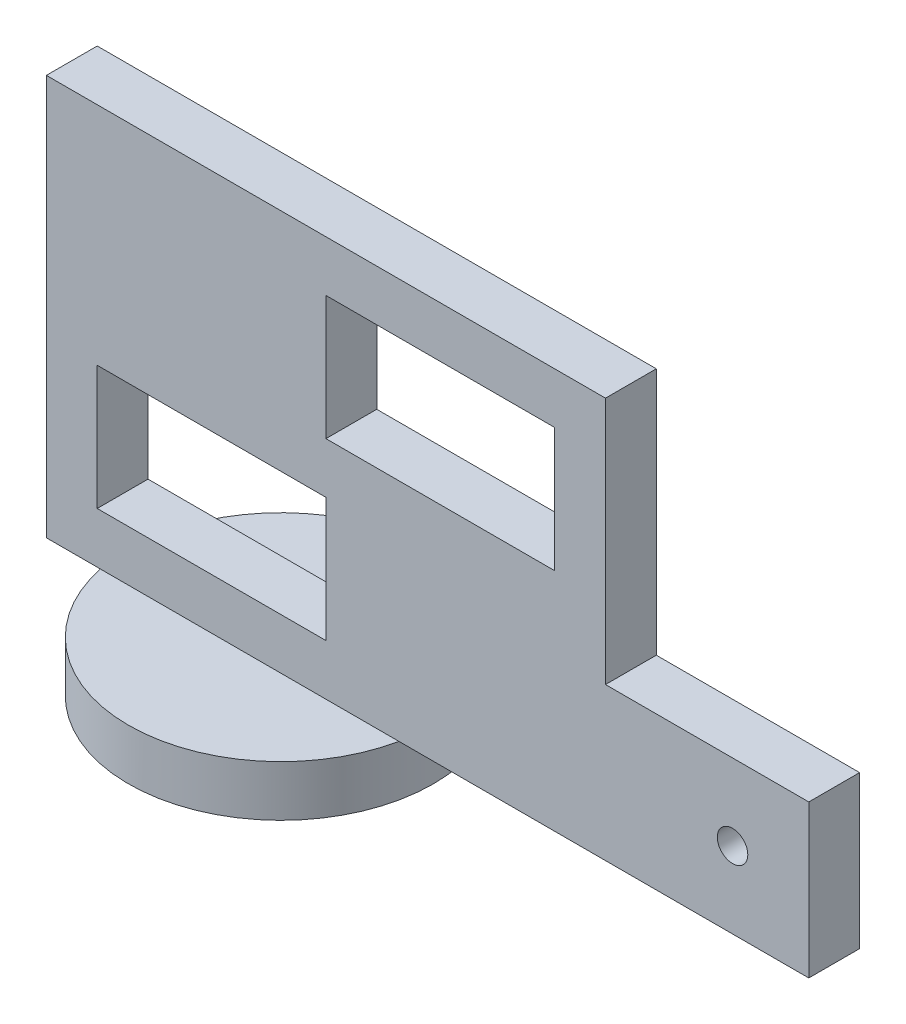
SolidWorks part; units mm, degrees
ref_plane "Front Plane" through (0, 0, 0) normal (0, 0, 1) x (1, 0, 0)
ref_plane "Top Plane" through (0, 0, 0) normal (0, 1, 0) x (1, 0, 0)
ref_plane "Right Plane" through (0, 0, 0) normal (1, 0, 0) x (0, 0, -1)
sketch "Sketch1" plane through (0, 0, 0) normal (0, 0, 1) x (1, 0, 0)
  line L1 (0, 0) -> (-55, 0)
  line L2 (0, 15) -> (0, 39.4)
  line L3 (0, 39.4) -> (-55, 39.4)
  line L4 (-55, 0) -> (-55, 39.4)
  line L5 (-50, 17.2) -> (-27.5, 17.2)
  line L6 (-50, 17.2) -> (-50, 5)
  line L7 (-50, 5) -> (-27.5, 5)
  line L8 (-27.5, 17.2) -> (-27.5, 5)
  line L9 (-27.5, 34.4) -> (-5, 34.4)
  line L10 (-27.5, 34.4) -> (-27.5, 22.2)
  line L11 (-27.5, 22.2) -> (-5, 22.2)
  line L12 (-5, 34.4) -> (-5, 22.2)
  line L13 (0, 0) -> (20, 0)
  line L15 (0, 15) -> (20, 15)
  line L16 (20, 0) -> (20, 15)
  circle A0 centre (12.5, 7.5) radius 1.5
  dimension "D13" = 3
  dimension "D14" = 7.5
  dimension "D15" = 7.5
  dimension "D1" = 22.5
  dimension "D2" = 12.2
  dimension "D3" = 22.5
  dimension "D4" = 12.2
  dimension "D5" = 5
  dimension "D6" = 5
  dimension "D7" = 5
  dimension "D8" = 0
  dimension "D9" = 5
  dimension "D10" = 5
  dimension "D11" = 20
  dimension "D12" = 15
extrude "Boss-Extrude1" add sketch "Sketch1" along normal blind 5
sketch "Sketch2" plane through (0, 0, 0) normal (0, -1, 0) x (1, 0, 0)
  line L0 (-55, 5) -> (-55, 0) construction
  circle A0 centre (-35, 1.9297) radius 15
  dimension "D1" = 30
  dimension "D2" = 20
extrude "Boss-Extrude2" add sketch "Sketch2" along normal blind 5
